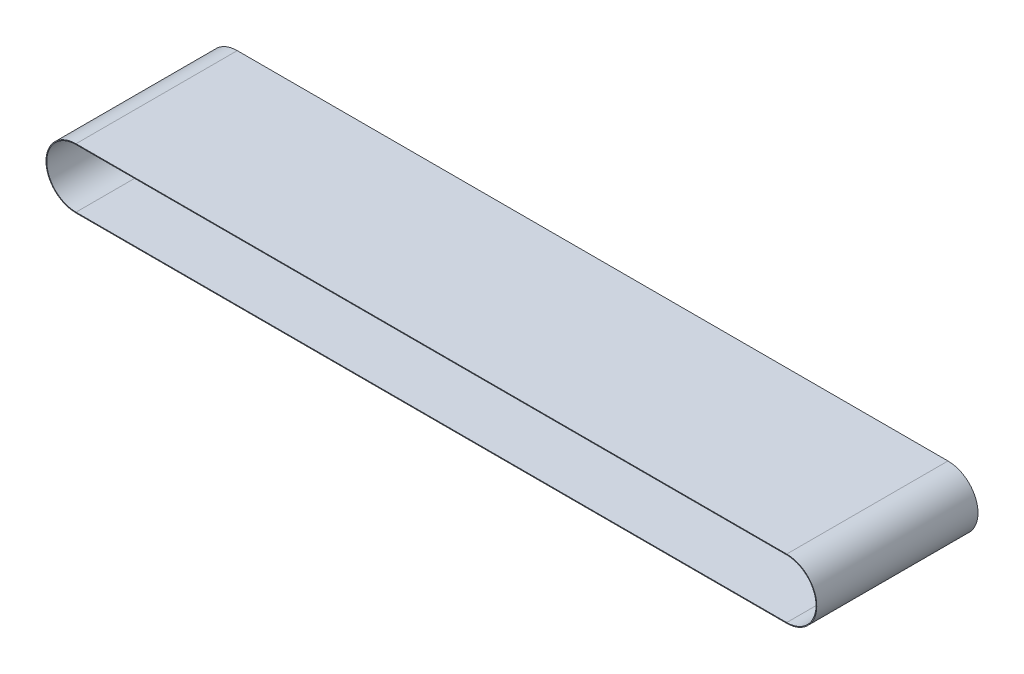
SolidWorks part; units mm, degrees
material "Náilon 101"
ref_plane "Plano frontal" through (0, 0, 0) normal (0, 0, 1) x (1, 0, 0)
ref_plane "Plano superior" through (0, 0, 0) normal (0, 1, 0) x (1, 0, 0)
ref_plane "Plano direito" through (0, 0, 0) normal (1, 0, 0) x (0, 0, -1)
sketch "Esboço1" plane through (0, 0, 0) normal (0, 0, 1) x (1, 0, 0)
  line L0 (-167.5, 0) -> (167.5, 0) construction
  line L1 (-167.5, 13.8) -> (167.5, 13.8)
  line L2 (-167.5, -13.8) -> (167.5, -13.8)
  line L3 (-167.5, 0) -> (167.5, 0) construction
  line L4 (-167.5, 14.15) -> (167.5, 14.15)
  line L5 (-167.5, -14.15) -> (167.5, -14.15)
  arc A0 (-167.5, 13.8) -> (-167.5, -13.8) centre (-167.5, 0) ccw
  arc A1 (167.5, -13.8) -> (167.5, 13.8) centre (167.5, 0) ccw
  arc A2 (-167.5, 14.15) -> (-167.5, -14.15) centre (-167.5, 0) ccw
  arc A3 (167.5, -14.15) -> (167.5, 14.15) centre (167.5, 0) ccw
  point P3 (0, 0)
  point P8 (0, 0)
  dimension "D2" = 13.8
  dimension "D3" = 14.15
  dimension "D1" = 335
extrude "Ressalto-extrusão1" add sketch "Esboço1" along normal blind 76
